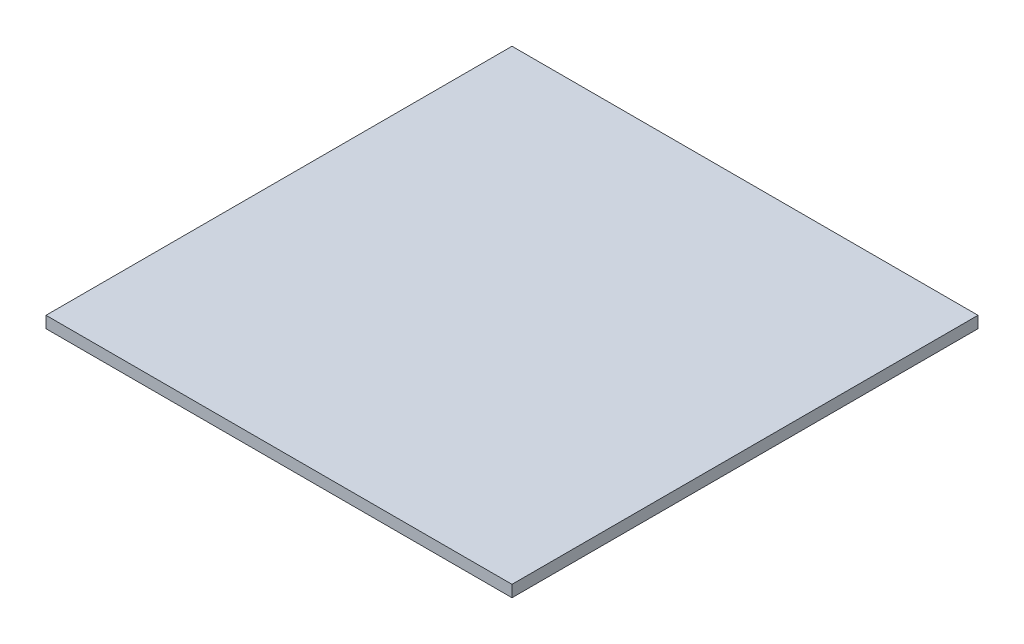
SolidWorks part; units mm, degrees
other "相机1"
material "PMMA"
ref_plane "前视基准面" through (0, 0, 0) normal (0, 0, 1) x (1, 0, 0)
ref_plane "上视基准面" through (0, 0, 0) normal (0, 1, 0) x (1, 0, 0)
ref_plane "右视基准面" through (0, 0, 0) normal (1, 0, 0) x (0, 0, -1)
sketch "草图1" plane through (0, 0, 0) normal (0, 1, 0) x (1, 0, 0)
  line L1 (-100, 100) -> (100, 100)
  line L2 (-100, 100) -> (-100, -100)
  line L3 (-100, -100) -> (100, -100)
  line L4 (100, 100) -> (100, -100)
  line L5 (-100, 100) -> (100, -100) construction
  line L6 (-100, -100) -> (100, 100) construction
  point P0 (0, 0)
  dimension "D1" = 200
  dimension "D2" = 200
extrude "凸台-拉伸1" add sketch "草图1" along normal blind 5
